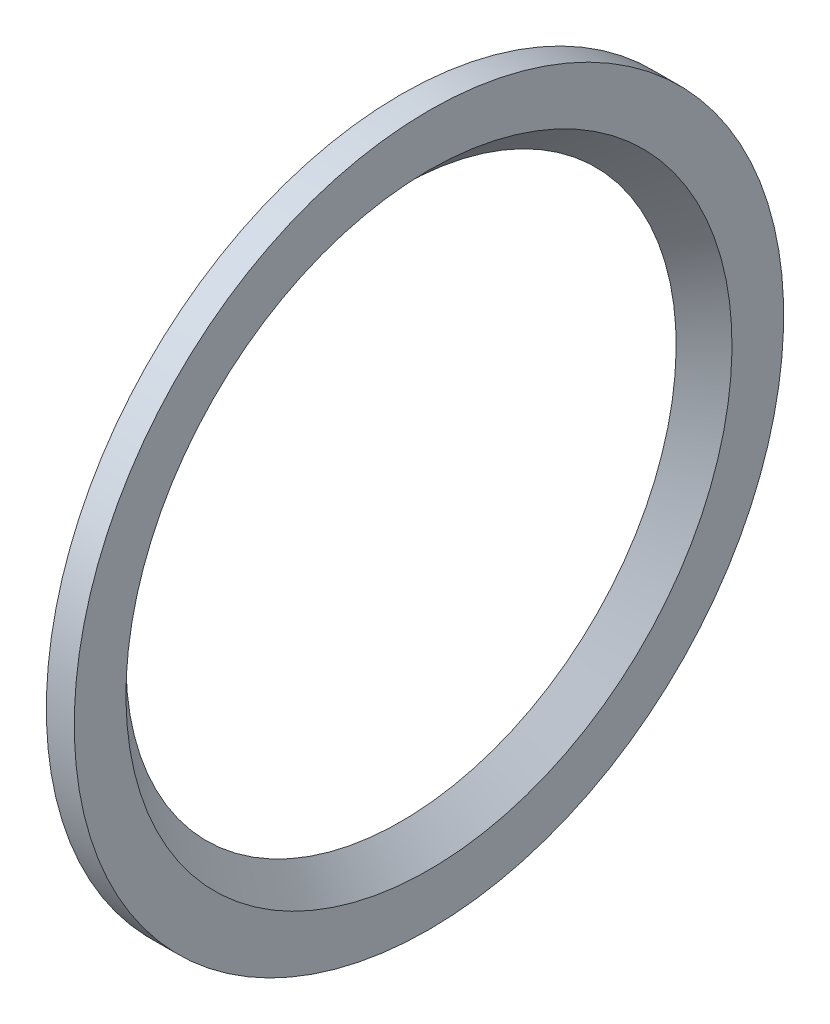
SolidWorks part; units mm, degrees
material "5052-H32"
ref_plane "Přední rovina" through (0, 0, 0) normal (0, 0, 1) x (1, 0, 0)
ref_plane "Horní rovina" through (0, 0, 0) normal (0, 1, 0) x (1, 0, 0)
ref_plane "Pravá rovina" through (0, 0, 0) normal (1, 0, 0) x (0, 0, -1)
sketch "Skica1" plane through (0, 0, 0) normal (0, 0, 1) x (1, 0, 0)
  line L0 (-217.05, -19.7) -> (-217.05, -25.4) construction
  line L1 (-215.05, -21.7) -> (-217.05, -19.7) construction
  line L2 (-215.05, -25.4) -> (-215.05, -21.7) construction
  line L3 (-217.05, -25.4) -> (-215.05, -25.4) construction
  line L4 (-217.05, -19.7) -> (-217.05, -25.4)
  line L5 (-215.05, -21.7) -> (-217.05, -19.7)
  line L6 (-215.05, -25.4) -> (-215.05, -21.7)
  line L7 (-217.05, -25.4) -> (-215.05, -25.4)
  line L8 (-67.4823, 0) -> (-363.0393, 0) construction
  line L9 (-67.4823, 0) -> (-363.0393, 0) construction
revolve "Rotovat1" add sketch "Skica1" angle 360 about L9
